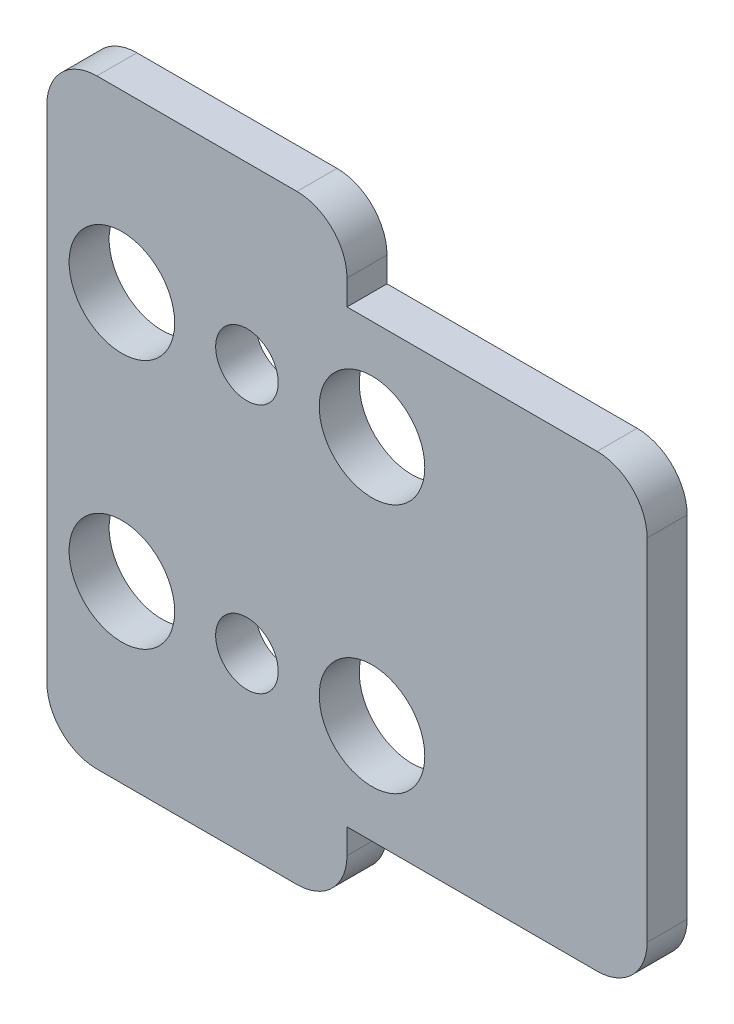
SolidWorks part; units mm, degrees
ref_plane "前视基准面" through (0, 0, 0) normal (0, 0, 1) x (1, 0, 0)
ref_plane "上视基准面" through (0, 0, 0) normal (0, 1, 0) x (1, 0, 0)
ref_plane "右视基准面" through (0, 0, 0) normal (1, 0, 0) x (0, 0, -1)
sketch "草图1" plane through (0, 0, 0) normal (0, 0, 1) x (1, 0, 0)
  line L0 (-378.0337, -12) -> (18431.0563, -12) construction
  line L1 (0, 0) -> (12, 0)
  line L2 (0, 0) -> (0, -24)
  line L3 (0, -24) -> (12, -24)
  line L4 (12, 0) -> (12, -24)
  line L6 (24, -3) -> (12, -3)
  line L7 (24, -3) -> (24, -21)
  line L8 (24, -21) -> (12, -21)
  line L9 (12, -3) -> (12, -21)
  line L10 (24, -3) -> (12, -21) construction
  line L11 (24, -21) -> (12, -3) construction
  circle A0 centre (3, -7) radius 2.11
  circle A1 centre (8, -7) radius 1.25
  circle A3 centre (13, -7) radius 2.11
  circle A4 centre (13, -17) radius 2.11
  circle A5 centre (8, -17) radius 1.25
  circle A6 centre (3, -17) radius 2.11
  point P8 (0, -12)
  point P9 (18, -12)
  dimension "D8" = 4.22
  dimension "D9" = 2.5
  dimension "D10" = 4.22
  dimension "D1" = 12
  dimension "D2" = 12
  dimension "D3" = 3
  dimension "D4" = 24
  dimension "D5" = 3
  dimension "D6" = 5
  dimension "D7" = 5
  dimension "D11" = 5
  dimension "D12" = 0
  dimension "D13" = 0
extrude "凸台-拉伸1" add sketch "草图1" along normal blind 1.6 contours L4 A4 A3 L1 L2 L3 A5 A1 A0 A6 | L4 A4 L8 L7 L6 A3
fillet "圆角1" radius 2 6 edges at (0, -24, 0.8) (12, -24, 0.8) (24, -21, 0.8) (24, -3, 0.8) (12, 0, 0.8) (0, 0, 0.8)
